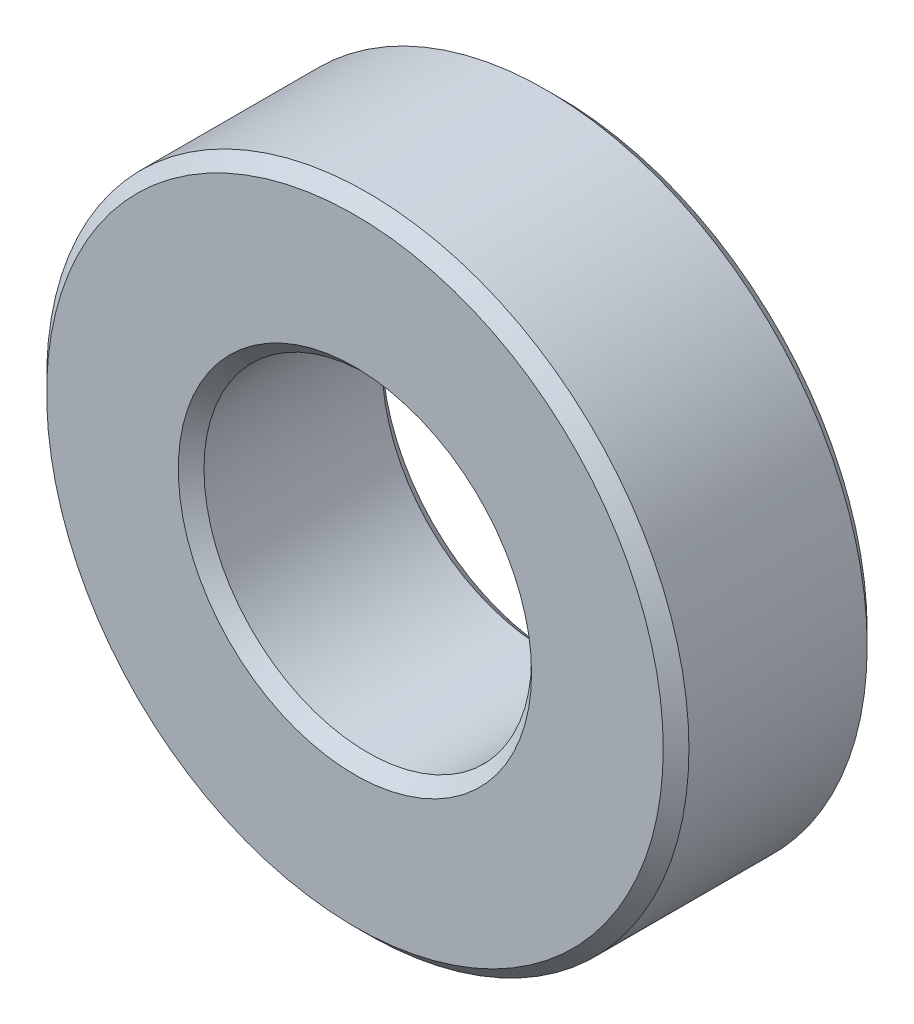
SolidWorks part; units mm, degrees
material "6061-T6 (SS)"
ref_plane "Front Plane" through (0, 0, 0) normal (0, 0, 1) x (1, 0, 0)
ref_plane "Top Plane" through (0, 0, 0) normal (0, 1, 0) x (1, 0, 0)
ref_plane "Right Plane" through (0, 0, 0) normal (1, 0, 0) x (0, 0, -1)
sketch "Sketch1" plane through (0, 0, 0) normal (0, 0, 1) x (1, 0, 0)
  circle A0 centre (0, 0) radius 2.55
  circle A1 centre (0, 0) radius 5
  dimension "D1" = 5.1
  dimension "D2" = 10
extrude "Boss-Extrude1" add sketch "Sketch1" along normal blind 3.175
chamfer "Chamfer1" distance 0.2 angle 45 4 edges at (5, 0, 0) (2.55, 0, 0) (2.55, 0, 3.175) (5, 0, 3.175)
